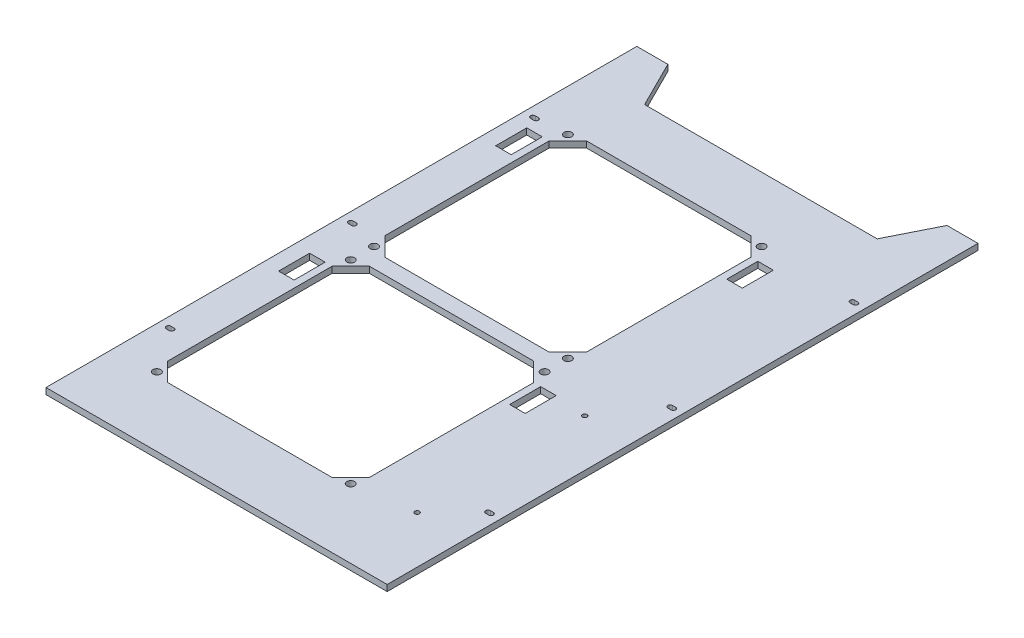
SolidWorks part; units mm, degrees
ref_plane "前基準面" through (0, 0, 0) normal (0, 0, 1) x (1, 0, 0)
ref_plane "上基準面" through (0, 0, 0) normal (0, 1, 0) x (1, 0, 0)
ref_plane "右基準面" through (0, 0, 0) normal (1, 0, 0) x (0, 0, -1)
ref_plane "平面1" through (0, 4, 0) normal (0, 1, 0) x (1, 0, 0)
sketch "草圖1" plane through (0, 4, 0) normal (0, 1, 0) x (1, 0, 0)
  line L0 (-75, 160.5) -> (-90, 190.5)
  line L1 (-90, 190.5) -> (-110, 190.5)
  line L2 (-110, 190.5) -> (-110, -190.5)
  line L3 (-110, -190.5) -> (110, -190.5)
  line L4 (110, -190.5) -> (110, 190.5)
  line L5 (110, 190.5) -> (90, 190.5)
  line L6 (90, 190.5) -> (75, 160.5)
  line L7 (75, 160.5) -> (-75, 160.5)
  line L8 (-104, 1.5) -> (-102, 1.5)
  line L9 (-102, -1.5) -> (-104, -1.5)
  line L10 (102, -116) -> (104, -116)
  line L11 (104, -119) -> (102, -119)
  line L12 (102, 1.5) -> (104, 1.5)
  line L13 (104, -1.5) -> (102, -1.5)
  line L14 (102, 119) -> (104, 119)
  line L15 (104, 116) -> (102, 116)
  line L16 (-104, -116) -> (-102, -116)
  line L17 (-102, -119) -> (-104, -119)
  line L18 (-104, 119) -> (-102, 119)
  line L19 (-102, 116) -> (-104, 116)
  line L20 (-85.5, 3.5) -> (-85.5, 109.5)
  line L21 (-85.5, 109.5) -> (-73.5, 121.5)
  line L22 (-73.5, 121.5) -> (32.5, 121.5)
  line L23 (32.5, 121.5) -> (44.5, 109.5)
  line L24 (44.5, 109.5) -> (44.5, 3.5)
  line L25 (44.5, 3.5) -> (32.5, -8.5)
  line L26 (32.5, -8.5) -> (-73.5, -8.5)
  line L27 (-73.5, -8.5) -> (-85.5, 3.5)
  line L28 (-85.5, -30.5) -> (-73.5, -18.5)
  line L29 (-73.5, -18.5) -> (32.5, -18.5)
  line L30 (32.5, -18.5) -> (44.5, -30.5)
  line L31 (44.5, -30.5) -> (44.5, -136.5)
  line L32 (44.5, -136.5) -> (32.5, -148.5)
  line L33 (32.5, -148.5) -> (-73.5, -148.5)
  line L34 (-73.5, -148.5) -> (-85.5, -136.5)
  line L35 (-85.5, -136.5) -> (-85.5, -30.5)
  line L36 (-100, 89.5) -> (-100, 109.5)
  line L37 (-100, 109.5) -> (-90, 109.5)
  line L38 (-90, 109.5) -> (-90, 89.5)
  line L39 (-90, 89.5) -> (-100, 89.5)
  line L40 (49, 109.5) -> (59, 109.5)
  line L41 (59, 109.5) -> (59, 89.5)
  line L42 (59, 89.5) -> (49, 89.5)
  line L43 (49, 89.5) -> (49, 109.5)
  line L44 (49, -30.5) -> (59, -30.5)
  line L45 (59, -30.5) -> (59, -50.5)
  line L46 (59, -50.5) -> (49, -50.5)
  line L47 (49, -50.5) -> (49, -30.5)
  line L48 (-100, -30.5) -> (-90, -30.5)
  line L49 (-90, -30.5) -> (-90, -50.5)
  line L50 (-90, -50.5) -> (-100, -50.5)
  line L51 (-100, -50.5) -> (-100, -30.5)
  arc A0 (-102, 1.5) -> (-102, -1.5) centre (-102, 0) cw
  arc A1 (-104, -1.5) -> (-104, 1.5) centre (-104, 0) cw
  arc A2 (104, -116) -> (104, -119) centre (104, -117.5) cw
  arc A3 (102, -119) -> (102, -116) centre (102, -117.5) cw
  arc A4 (104, 1.5) -> (104, -1.5) centre (104, 0) cw
  arc A5 (102, -1.5) -> (102, 1.5) centre (102, 0) cw
  arc A6 (104, 119) -> (104, 116) centre (104, 117.5) cw
  arc A7 (102, 116) -> (102, 119) centre (102, 117.5) cw
  arc A8 (-102, -116) -> (-102, -119) centre (-102, -117.5) cw
  arc A9 (-104, -119) -> (-104, -116) centre (-104, -117.5) cw
  arc A10 (-102, 119) -> (-102, 116) centre (-102, 117.5) cw
  arc A11 (-104, 116) -> (-104, 119) centre (-104, 117.5) cw
  circle A12 centre (79.5, -32.62) radius 1.5
  circle A13 centre (79.5, -140.62) radius 1.5
  circle A14 centre (-83, -6) radius 2.5
  circle A15 centre (42, -21) radius 2.5
  circle A16 centre (42, -146) radius 2.5
  circle A17 centre (-83, -146) radius 2.5
  circle A18 centre (-83, 119) radius 2.5
  circle A19 centre (42, -6) radius 2.5
  circle A20 centre (-83, -21) radius 2.5
  circle A21 centre (42, 119) radius 2.5
extrude "填料-伸長1" add sketch "草圖1" against normal blind 4
